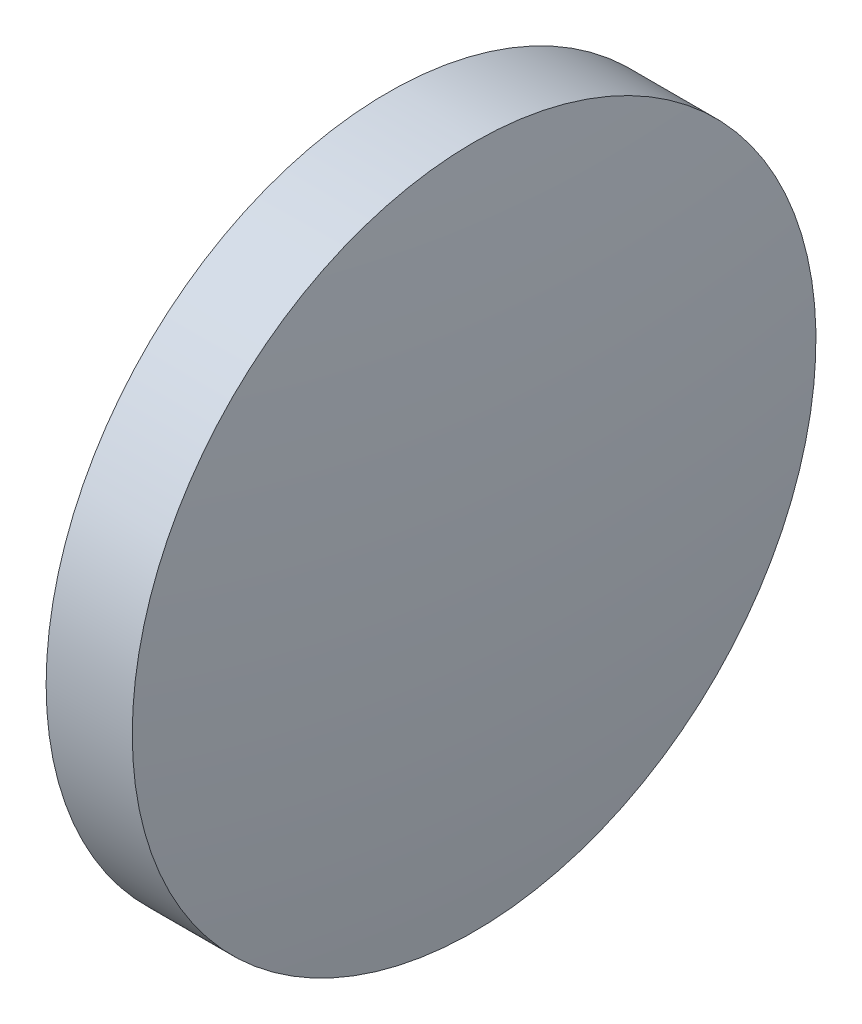
SolidWorks part; units mm, degrees
ref_plane "前视基准面" through (0, 0, 0) normal (0, 0, 1) x (1, 0, 0)
ref_plane "上视基准面" through (0, 0, 0) normal (0, 1, 0) x (1, 0, 0)
ref_plane "右视基准面" through (0, 0, 0) normal (1, 0, 0) x (0, 0, -1)
sketch "草图1" plane through (0, 0, 0) normal (0, 0, 1) x (1, 0, 0)
  line L0 (473.6823, 287.4787) -> (492.4783, 287.4787) construction
  line L1 (479.4205, 287.4787) -> (479.4205, 300.1787)
  line L2 (483.4205, 287.4787) -> (479.4205, 287.4787)
  line L5 (479.4205, 300.1787) -> (482.6205, 300.1787)
  arc A0 (483.4205, 287.4787) -> (482.6205, 300.1787) centre (382.2142, 287.4787) ccw
revolve "旋转1" add sketch "草图1" angle 360 about L0
